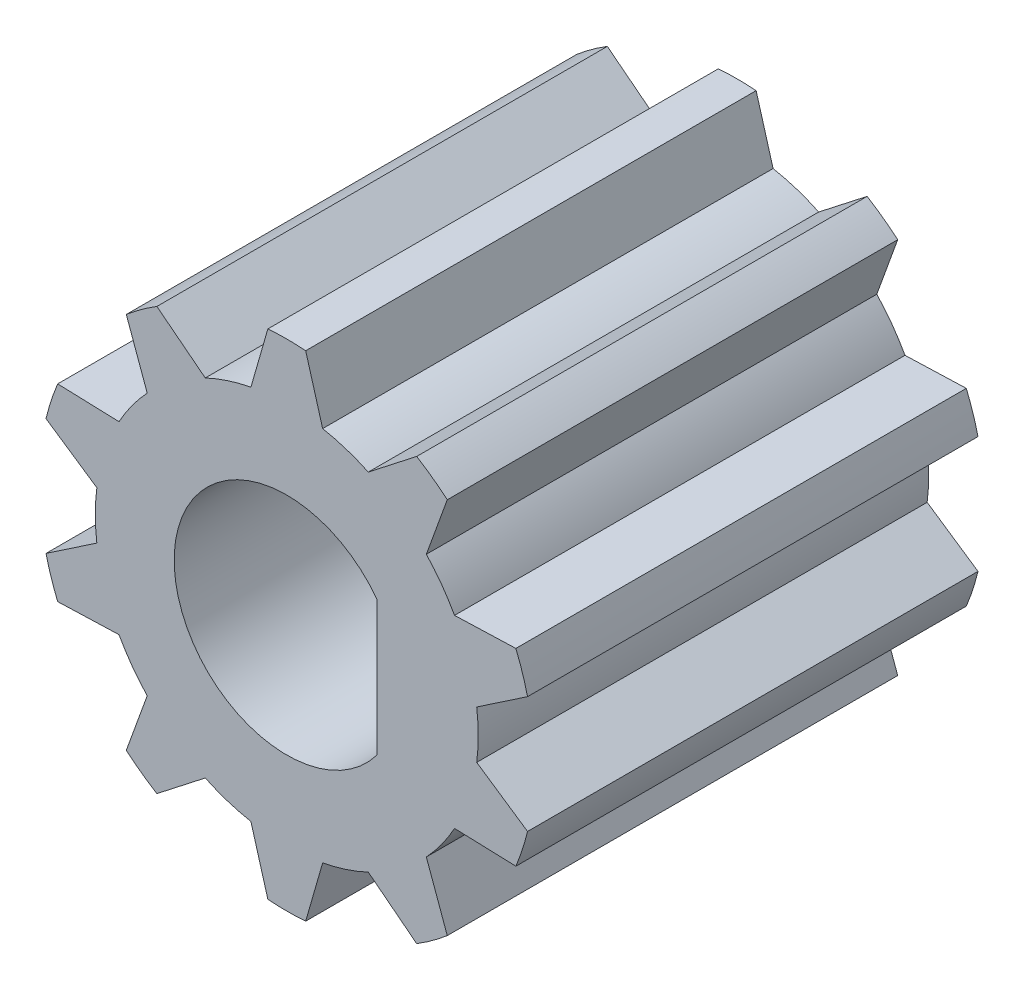
SolidWorks part; units mm, degrees
ref_plane "Front Plane" through (0, 0, 0) normal (0, 0, 1) x (1, 0, 0)
ref_plane "Top Plane" through (0, 0, 0) normal (0, 1, 0) x (1, 0, 0)
ref_plane "Right Plane" through (0, 0, 0) normal (1, 0, 0) x (0, 0, -1)
sketch "Sketch1" plane through (0, 0, 0) normal (0, 0, 1) x (1, 0, 0)
  line L0 (0, 0) -> (0, 4.25) construction
  line L1 (0, 4.25) -> (0, 5.5) construction
  line L2 (-0.7964, 4.1747) -> (-0.4197, 5.484)
  line L3 (0.4197, 5.484) -> (0.7964, 4.1747)
  line L4 (1.8095, 3.8455) -> (2.8839, 4.6833)
  line L5 (3.5629, 4.1899) -> (3.0982, 2.9093)
  line L6 (3.7243, 2.0475) -> (5.0859, 2.0938)
  line L7 (5.3453, 1.2955) -> (4.2165, 0.5326)
  line L8 (4.2165, -0.5326) -> (5.3453, -1.2955)
  line L9 (5.0859, -2.0938) -> (3.7243, -2.0475)
  line L10 (3.0982, -2.9093) -> (3.5629, -4.1899)
  line L11 (2.8839, -4.6833) -> (1.8095, -3.8455)
  line L12 (0.7964, -4.1747) -> (0.4197, -5.484)
  line L13 (-0.4197, -5.484) -> (-0.7964, -4.1747)
  line L14 (-1.8095, -3.8455) -> (-2.8839, -4.6833)
  line L15 (-3.5629, -4.1899) -> (-3.0982, -2.9093)
  line L16 (-3.7243, -2.0475) -> (-5.0859, -2.0938)
  line L17 (-5.3453, -1.2955) -> (-4.2165, -0.5326)
  line L18 (-4.2165, 0.5326) -> (-5.3453, 1.2955)
  line L19 (-5.0859, 2.0938) -> (-3.7243, 2.0475)
  line L20 (-3.0982, 2.9093) -> (-3.5629, 4.1899)
  line L21 (-2.8839, 4.6833) -> (-1.8095, 3.8455)
  line L22 (-2.5, 0) -> (2, 0) construction
  line L23 (2, 1.5) -> (2, -1.5)
  circle A0 centre (0, 0) radius 4.25 construction
  circle A1 centre (0, 0) radius 5.5 construction
  arc A2 (-0.7964, 4.1747) -> (0.7964, 4.1747) centre (0, 0) cw construction
  arc A3 (-0.4197, 5.484) -> (0.4197, 5.484) centre (0, 0) cw
  arc A4 (2.8839, 4.6833) -> (3.5629, 4.1899) centre (0, 0) cw
  arc A5 (5.0859, 2.0938) -> (5.3453, 1.2955) centre (0, 0) cw
  arc A6 (5.3453, -1.2955) -> (5.0859, -2.0938) centre (0, 0) cw
  arc A7 (3.5629, -4.1899) -> (2.8839, -4.6833) centre (0, 0) cw
  arc A8 (0.4197, -5.484) -> (-0.4197, -5.484) centre (0, 0) cw
  arc A9 (-2.8839, -4.6833) -> (-3.5629, -4.1899) centre (0, 0) cw
  arc A10 (-5.0859, -2.0938) -> (-5.3453, -1.2955) centre (0, 0) cw
  arc A11 (-5.3453, 1.2955) -> (-5.0859, 2.0938) centre (0, 0) cw
  arc A12 (-3.5629, 4.1899) -> (-2.8839, 4.6833) centre (0, 0) cw
  arc A13 (-3.7243, 2.0475) -> (-3.0982, 2.9093) centre (0, 0) cw
  arc A14 (-1.8095, 3.8455) -> (-0.7964, 4.1747) centre (0, 0) cw
  arc A15 (0.7964, 4.1747) -> (1.8095, 3.8455) centre (0, 0) cw
  arc A16 (3.0982, 2.9093) -> (3.7243, 2.0475) centre (0, 0) cw
  arc A17 (4.2165, 0.5326) -> (4.2165, -0.5326) centre (0, 0) cw
  arc A18 (3.7243, -2.0475) -> (3.0982, -2.9093) centre (0, 0) cw
  arc A19 (1.8095, -3.8455) -> (0.7964, -4.1747) centre (0, 0) cw
  arc A20 (-0.7964, -4.1747) -> (-1.8095, -3.8455) centre (0, 0) cw
  arc A21 (-3.0982, -2.9093) -> (-3.7243, -2.0475) centre (0, 0) cw
  arc A22 (-4.2165, -0.5326) -> (-4.2165, 0.5326) centre (0, 0) cw
  arc A23 (2, 1.5) -> (2, -1.5) centre (0, 0) ccw
  point P48 (0, 0)
  point P53 (2, 0)
  point P68 (0, 0)
  dimension "D1" = 8.5
  dimension "D2" = 11
  dimension "D3" = 0.8
  dimension "D5" = 0.42
  dimension "D8" = 10
  dimension "D9" = 5
  dimension "D4" = 0.8
  dimension "D6" = 0.42
  dimension "D7" = 10
  dimension "D10" = 4.5
extrude "Boss-Extrude1" add sketch "Sketch1" along normal blind 10
